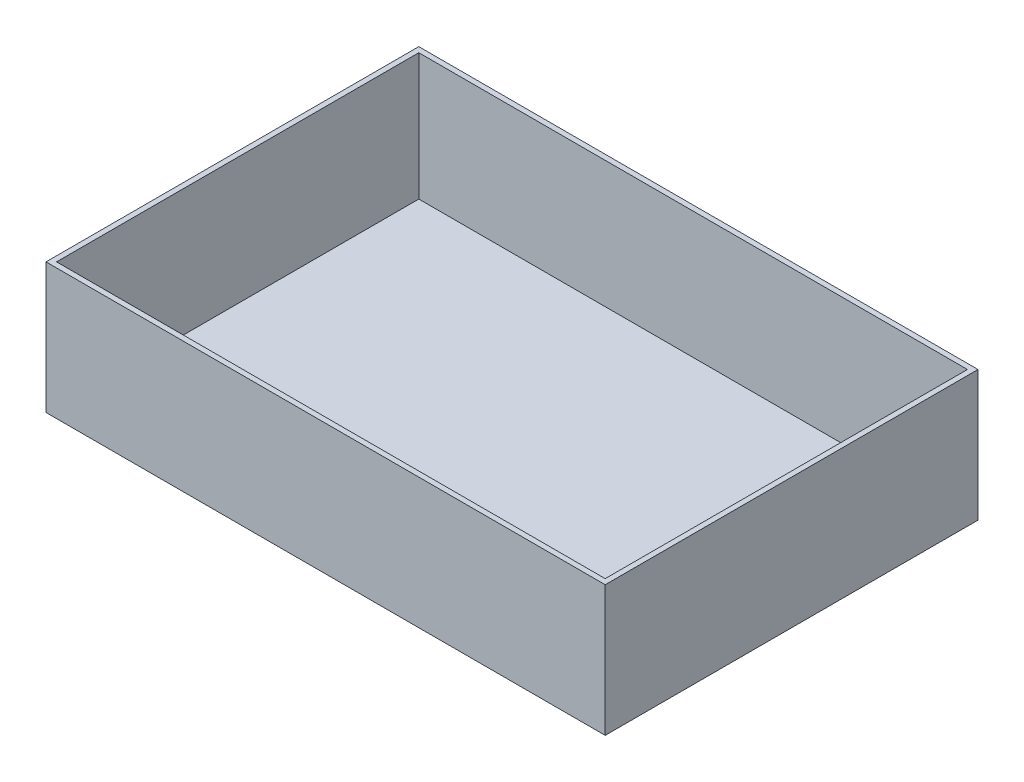
SolidWorks part; units mm, degrees
ref_plane "Front Plane" through (0, 0, 0) normal (0, 0, 1) x (1, 0, 0)
ref_plane "Top Plane" through (0, 0, 0) normal (0, 1, 0) x (1, 0, 0)
ref_plane "Right Plane" through (0, 0, 0) normal (1, 0, 0) x (0, 0, -1)
sketch "Sketch1" plane through (0, 0, 0) normal (0, 1, 0) x (1, 0, 0)
  line L0 (0, 0) -> (28.2843, 28.2843) construction
  line L1 (0, 0) -> (3000, 0)
  line L2 (0, 0) -> (0, 2000)
  line L3 (0, 2000) -> (3000, 2000)
  line L4 (3000, 0) -> (3000, 2000)
  line L6 (28.2843, 28.2843) -> (2971.7157, 28.2843)
  line L7 (28.2843, 28.2843) -> (28.2843, 1971.7157)
  line L8 (28.2843, 1971.7157) -> (2971.7157, 1971.7157)
  line L9 (2971.7157, 28.2843) -> (2971.7157, 1971.7157)
  dimension "D1" = 3000
  dimension "D2" = 2000
  dimension "D3" = 45
  dimension "D4" = 40
  dimension "D5" = 40
  dimension "D6" = 40
extrude "Boss-Extrude2" add sketch "Sketch1" along normal blind 700
sketch "Sketch2" plane through (0, 0, 0) normal (0, 1, 0) x (1, 0, 0)
  line L1 (28.2843, 1971.7157) -> (2971.7157, 1971.7157)
  line L2 (28.2843, 1971.7157) -> (28.2843, 28.2843)
  line L3 (28.2843, 28.2843) -> (2971.7157, 28.2843)
  line L4 (2971.7157, 1971.7157) -> (2971.7157, 28.2843)
extrude "Boss-Extrude3" add sketch "Sketch2" along normal blind 20
